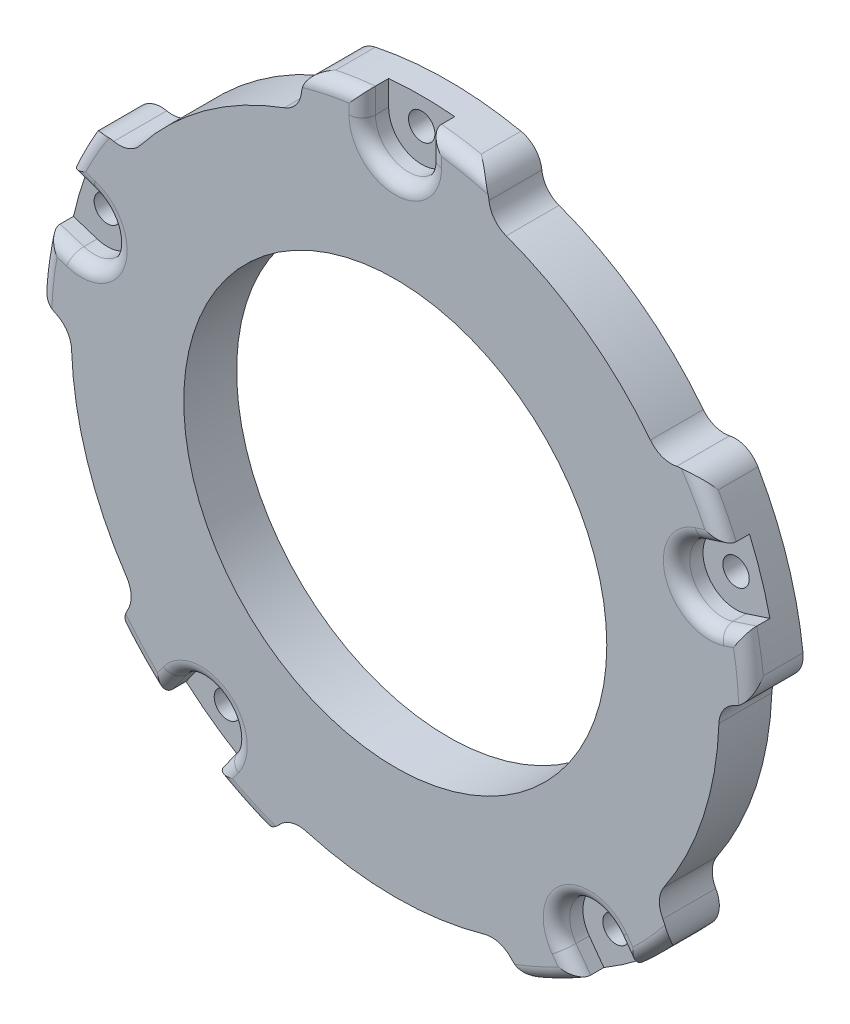
SolidWorks part; units mm, degrees
ref_plane "前视基准面" through (0, 0, 0) normal (0, 0, 1) x (1, 0, 0)
ref_plane "上视基准面" through (0, 0, 0) normal (0, 1, 0) x (1, 0, 0)
ref_plane "右视基准面" through (0, 0, 0) normal (1, 0, 0) x (0, 0, -1)
sketch "草图1" plane through (0, 0, 0) normal (0, 0, 1) x (1, 0, 0)
  circle A0 centre (0, 0) radius 25
  circle A1 centre (0, 0) radius 16
  circle A2 centre (21.8743, -7.1074) radius 1
  circle A3 centre (13.5191, -18.6074) radius 1
  circle A4 centre (0, -23) radius 1
  circle A5 centre (-13.5191, -18.6074) radius 1
  circle A6 centre (-21.8743, -7.1074) radius 1
  circle A7 centre (-21.8743, 7.1074) radius 1
  circle A8 centre (-13.5191, 18.6074) radius 1
  circle A9 centre (0, 23) radius 1
  circle A10 centre (13.5191, 18.6074) radius 1
  circle A11 centre (21.8743, 7.1074) radius 1
  point P24 (0, 0)
extrude "凸台-拉伸1" add sketch "草图1" along normal blind 4
sketch "草图2" plane through (0, 0, 0) normal (0, 0, -1) x (-1, 0, 0)
  circle A0 centre (0, 0) radius 27
  circle A1 centre (0, 0) radius 25
extrude "凸台-拉伸2" add sketch "草图2" against normal up to surface (4 mm away) up to face at (14.5191, 18.6074, 4)
sketch "草图3" plane through (0, 0, 0) normal (0, 0, -1) x (-1, 0, 0)
  circle A1 centre (-21.8743, 7.1074) radius 1 construction
  circle A2 centre (-21.8743, -7.1074) radius 1 construction
  circle A3 centre (-13.5191, -18.6074) radius 1 construction
  circle A4 centre (0, -23) radius 1 construction
  circle A5 centre (13.5191, -18.6074) radius 1 construction
  circle A6 centre (21.8743, -7.1074) radius 1 construction
  circle A7 centre (21.8743, 7.1074) radius 1 construction
  circle A8 centre (0, 23) radius 1 construction
  circle A9 centre (-13.5191, 18.6074) radius 1 construction
  circle A10 centre (-21.8743, 7.1074) radius 1
  circle A11 centre (-21.8743, -7.1074) radius 1
  circle A12 centre (-13.5191, -18.6074) radius 1
  circle A13 centre (0, -23) radius 1
  circle A14 centre (13.5191, -18.6074) radius 1
  circle A15 centre (21.8743, -7.1074) radius 1
  circle A16 centre (21.8743, 7.1074) radius 1
  circle A17 centre (0, 23) radius 1
  circle A18 centre (-13.5191, 18.6074) radius 1
  circle A19 centre (13.5191, 18.6074) radius 1 construction
  circle A20 centre (13.5191, 18.6074) radius 1
extrude "凸台-拉伸3" add sketch "草图3" against normal up to surface (4 mm away) up to face at (14.5191, 18.6074, 4)
sketch "草图4" plane through (0, 0, 0) normal (0, 0, -1) x (-1, 0, 0)
  circle A0 centre (0, 25) radius 1
  circle A1 centre (23.7764, 7.7254) radius 1
  circle A2 centre (14.6946, -20.2254) radius 1
  circle A3 centre (-14.6946, -20.2254) radius 1
  circle A4 centre (-23.7764, 7.7254) radius 1
  point P14 (0, 0)
extrude "切除-拉伸1" cut sketch "草图4" against normal blind 10
sketch "草图7" plane through (0, 0, 4) normal (0, 0, 1) x (1, 0, 0)
  line L0 (-13.7795, -23.2191) -> (-12.6721, -21.6949)
  line L1 (-17.8246, -20.2802) -> (-16.7172, -18.756)
  line L2 (17.8246, -20.2802) -> (16.7172, -18.756)
  line L3 (-26.3408, 5.93) -> (-24.549, 5.3478)
  line L4 (13.7795, -23.2191) -> (12.6721, -21.6949)
  line L5 (-24.7957, 10.6853) -> (-23.0039, 10.1031)
  line L7 (-2.5, 26.884) -> (-2.5, 25)
  line L8 (2.5, 26.884) -> (2.5, 25)
  line L9 (24.7957, 10.6853) -> (23.0039, 10.1031)
  line L10 (26.3408, 5.93) -> (24.549, 5.3478)
  arc A0 (16.7172, -18.756) -> (12.6721, -21.6949) centre (14.6946, -20.2254) ccw
  circle A2 centre (0, 0) radius 27 construction
  circle A3 centre (0, 0) radius 27
  arc A4 (-12.6721, -21.6949) -> (-16.7172, -18.756) centre (-14.6946, -20.2254) ccw
  arc A5 (-24.549, 5.3478) -> (-23.0039, 10.1031) centre (-23.7764, 7.7254) ccw
  arc A6 (-2.5, 25) -> (2.5, 25) centre (0, 25) ccw
  arc A7 (23.0039, 10.1031) -> (24.549, 5.3478) centre (23.7764, 7.7254) ccw
  point P32 (0, 0)
  circle M7 centre (0, 25) radius 1
  circle M8 centre (-23.7764, 7.7254) radius 1
  circle M9 centre (-14.6946, -20.2254) radius 1
  circle M10 centre (14.6946, -20.2254) radius 1
  circle M11 centre (23.7764, 7.7254) radius 1
  circle M13 centre (0, 0) radius 27
extrude "切除-拉伸2" cut sketch "草图7" against normal blind 2 contours L2 A0 L4 M13 M10 | L0 A4 L1 M13 M9 | L9 A7 L10 M13 M11 | L3 A5 L5 M13 M8 | L7 A6 L8 M13 M7
fillet "圆角1" radius 1 20 edges at (-13.2252, -18.2029, 4) (-17.2709, -19.5181, 4) (-25.6785, -8.3435, 4) (-25.4449, 5.6389, 4) (-21.3988, 6.9529, 4) (-23.8998, 10.3942, 4) (-15.8702, 21.8435, 4) (-2.5, 25.942, 4) (0, 22.5, 4) (2.5, 25.942, 4) (15.8702, 21.8435, 4) (23.8998, 10.3942, 4) (21.3988, 6.9529, 4) (25.4449, 5.6389, 4) (25.6785, -8.3435, 4) (17.2709, -19.5181, 4) (13.2252, -18.2029, 4) (13.2258, -22.457, 4) (0, -27, 4) (-13.2258, -22.457, 4)
sketch "草图8" plane through (0, 0, 4) normal (0, 0, 1) x (1, 0, 0)
  line L0 (21.1533, 14.3366) -> (20.0835, 14.0322)
  arc A0 (-19.9922, -18.147) -> (-11.0809, -24.6214) centre (0, 0) ccw
  arc A1 (-11.0809, -24.6214) -> (-8.7753, -24.1375) centre (-10.2601, -22.7976) ccw
  arc A2 (-6.7402, -23.5546) -> (-8.7753, -24.1375) centre (-7.2905, -25.4774) ccw
  arc A3 (-6.7402, -23.5546) -> (6.7402, -23.5546) centre (0, 0) ccw
  arc A4 (8.7753, -24.1375) -> (6.7402, -23.5546) centre (7.2905, -25.4774) ccw
  arc A5 (8.7753, -24.1375) -> (11.0809, -24.6214) centre (10.2601, -22.7976) ccw
  arc A6 (11.0809, -24.6214) -> (19.9922, -18.147) centre (0, 0) ccw
  arc A7 (19.9922, -18.147) -> (20.2444, -15.8047) centre (18.5113, -16.8027) ccw
  arc A8 (20.3189, -13.6891) -> (20.2444, -15.8047) centre (21.9776, -14.8066) ccw
  arc A9 (20.3189, -13.6891) -> (24.4846, -0.8684) centre (0, 0) ccw
  arc A10 (25.6678, 0.8869) -> (24.4846, -0.8684) centre (26.4833, -0.9393) ccw
  arc A11 (25.6678, 0.8869) -> (26.8405, 2.9301) centre (24.8524, 2.7131) ccw
  arc A12 (26.8405, 2.9301) -> (23.4367, 13.406) centre (0, 0) ccw
  arc A13 (23.4367, 13.406) -> (21.1533, 14.3366) centre (21.7007, 12.4129) ccw
  arc A14 (20.0835, 14.0322) -> (8.3921, 23.0179) centre (0, 0) ccw
  arc A15 (7.0883, 24.6856) -> (8.3921, 23.0179) centre (9.0772, 24.8969) ccw
  arc A16 (7.0883, 24.6856) -> (5.5075, 26.4323) centre (5.0995, 24.4744) ccw
  arc A17 (5.5075, 26.4323) -> (-5.5075, 26.4323) centre (0, 0) ccw
  arc A18 (-5.5075, 26.4323) -> (-7.0883, 24.6856) centre (-5.0995, 24.4744) ccw
  arc A19 (-8.3921, 23.0179) -> (-7.0883, 24.6856) centre (-9.0772, 24.8969) ccw
  arc A20 (-8.3921, 23.0179) -> (-19.298, 15.0943) centre (0, 0) ccw
  arc A21 (-21.287, 14.3697) -> (-19.298, 15.0943) centre (-20.8734, 16.3265) ccw
  arc A22 (-21.287, 14.3697) -> (-23.4367, 13.406) centre (-21.7007, 12.4129) ccw
  arc A23 (-23.4367, 13.406) -> (-26.8405, 2.9301) centre (0, 0) ccw
  arc A24 (-26.8405, 2.9301) -> (-25.6678, 0.8869) centre (-24.8524, 2.7131) ccw
  arc A25 (-24.4846, -0.8684) -> (-25.6678, 0.8869) centre (-26.4833, -0.9393) ccw
  arc A26 (-24.4846, -0.8684) -> (-20.3189, -13.6891) centre (0, 0) ccw
  arc A27 (-20.2444, -15.8047) -> (-20.3189, -13.6891) centre (-21.9776, -14.8066) ccw
  arc A28 (-20.2444, -15.8047) -> (-19.9922, -18.147) centre (-18.5113, -16.8027) ccw
  circle A29 centre (0, 0) radius 27
  arc M35 (-12.3118, -22.9002) -> (12.3118, -22.9002) centre (0, 0) ccw
  arc M39 (17.9749, -18.7857) -> (25.584, 4.6326) centre (0, 0) ccw
  arc M43 (23.4208, 11.29) -> (3.5, 25.7633) centre (0, 0) ccw
  arc M47 (-3.5, 25.7633) -> (-23.4208, 11.29) centre (0, 0) ccw
  arc M51 (-25.584, 4.6326) -> (-17.9749, -18.7857) centre (0, 0) ccw
extrude "切除-拉伸3" cut sketch "草图8" against normal blind 12.07 contours A28 A27 A26 A25 A24 M51 | A5 A4 A3 A2 A1 M35 | A1 A29 A5 M35 | A24 A29 A28 M51 | A11 A10 A9 A8 A7 M39 | A16 A15 A14 L0 A13 M43 | A13 A29 A16 M43 | A7 A29 A11 M39 | A22 A21 A20 A19 A18 M47 | A18 A29 A22 M47
fillet "圆角2" radius 2 1 edges at (20.0835, 14.0322, 2)
